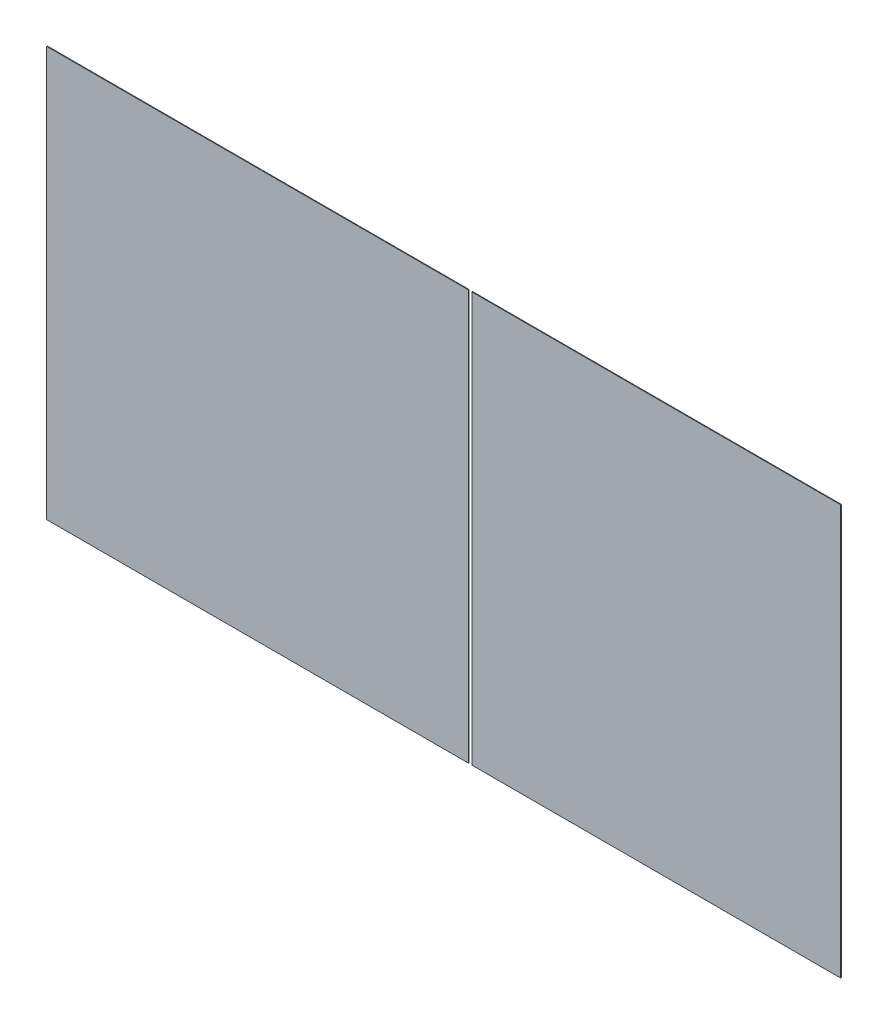
SolidWorks part; units mm, degrees
ref_plane "前视基准面" through (0, 0, 0) normal (0, 0, 1) x (1, 0, 0)
ref_plane "上视基准面" through (0, 0, 0) normal (0, 1, 0) x (1, 0, 0)
ref_plane "右视基准面" through (0, 0, 0) normal (1, 0, 0) x (0, 0, -1)
sketch "草图1" plane through (0, 0, 0) normal (0, 0, 1) x (1, 0, 0)
  line L1 (563.7593, -291.0748) -> (-1214.2407, -291.0748)
  line L2 (563.7593, -291.0748) -> (563.7593, 626.9252)
  line L3 (563.7593, 626.9252) -> (-1214.2407, 626.9252)
  line L4 (-1214.2407, -291.0748) -> (-1214.2407, 626.9252)
  line L5 (563.7593, -291.0748) -> (-1214.2407, 626.9252) construction
  line L6 (-2126.3092, -509.7136) -> (-1214.2407, -291.0748) construction
  point P0 (0, 0)
  dimension "D2" = 1778
  dimension "D3" = 918
extrude "凸台-拉伸1" add sketch "草图1" along normal blind 1.5
sketch "草图2" plane through (0, 0, 1.5) normal (0, 0, 1) x (1, 0, 0)
  line L1 (-262.2996, 882.7454) -> (-270.0681, 882.7454)
  line L2 (-262.2996, 882.7454) -> (-262.2996, -761.2216)
  line L3 (-262.2996, -761.2216) -> (-270.0681, -761.2216)
  line L4 (-270.0681, 882.7454) -> (-270.0681, -761.2216)
extrude "切除-拉伸1" cut sketch "草图2" against normal through all
